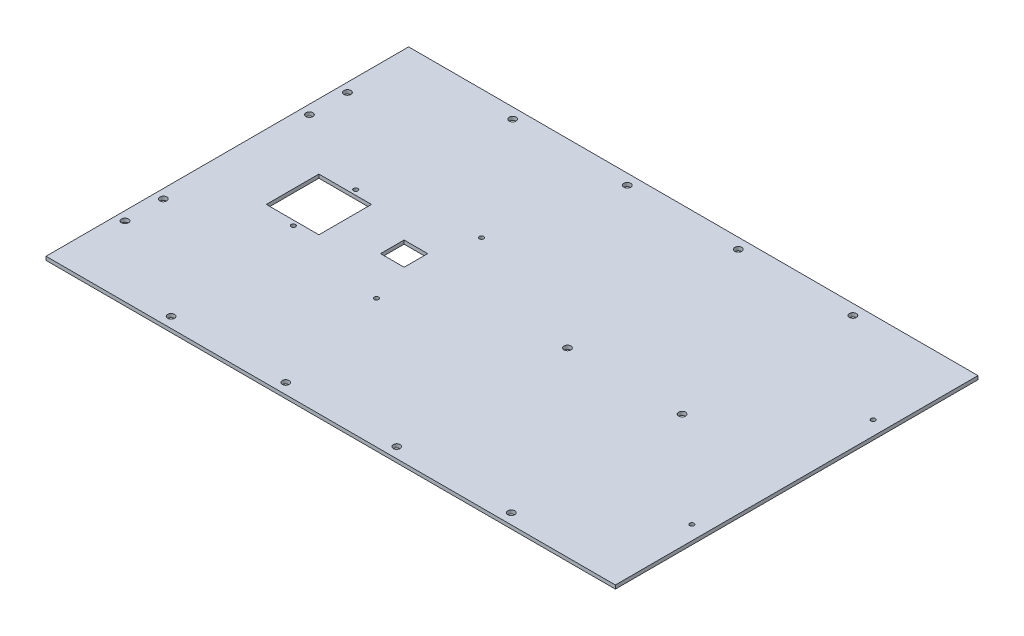
SolidWorks part; units mm, degrees
ref_plane "Front Plane" through (0, 0, 0) normal (0, 0, 1) x (1, 0, 0)
ref_plane "Top Plane" through (0, 0, 0) normal (0, 1, 0) x (1, 0, 0)
ref_plane "Right Plane" through (0, 0, 0) normal (1, 0, 0) x (0, 0, -1)
sketch "Sketch1" plane through (0, 0, 0) normal (0, 1, 0) x (1, 0, 0)
  line L0 (0, 63.5) -> (0, -63.5)
  line L1 (-199.39, 63.5) -> (199.39, 63.5)
  line L2 (-199.39, 63.5) -> (-199.39, -63.5)
  line L3 (-199.39, -63.5) -> (199.39, -63.5)
  line L4 (199.39, 63.5) -> (199.39, -63.5)
  dimension "D1" = 398.78
  dimension "D2" = 127
extrude "Boss-Extrude1" add sketch "Sketch1" along normal blind 2.54 contours L2 L3 L0 L1 | L4 L1 L0 L3
hole_wizard "#11 (0.191) Diameter Hole1" positions "Sketch6" profile "Sketch5" hole size "#11" standard "ANSI Inch" end condition through all
sketch "Sketch6" plane through (0, 2.54, 0) normal (0, 1, 0) x (1, 0, 0)
  line L0 (-199.39, 63.5) -> (-199.39, -63.5) construction
  line L1 (-199.39, -63.5) -> (199.39, -63.5) construction
  point P0 (-193.167, -14.4018)
  point P2 (-193.04, 12.3444)
  dimension "D1" = 6.223
  dimension "D2" = 49.0982
  dimension "D4" = 75.8444
sketch "Sketch5" plane through (-193.167, 2.54, 14.4018) normal (1, 0, 0) x (0, 0, 1)
  line L0 (0, 0) -> (0, 2.54)
  line L1 (0, 2.54) -> (2.4257, 2.54)
  line L2 (2.4257, 2.54) -> (2.4257, 0)
  line L5 (2.4257, 0) -> (0, 0)
  line L11 (0, -6.35) -> (0, 107.95) construction
  dimension "Thru Hole Dia." = 4.8514
  dimension "Thru Hole Depth" = 2.54
sketch "Sketch8" plane through (0, 2.54, 0) normal (0, 1, 0) x (1, 0, 0)
  line L0 (-199.39, 63.5) -> (199.39, 63.5) construction
  line L1 (-153.67, 63.5) -> (-116.84, 63.5)
  line L2 (-153.67, 63.5) -> (-153.67, 45.085)
  line L3 (-153.67, 45.085) -> (-116.84, 45.085)
  line L4 (-116.84, 63.5) -> (-116.84, 45.085)
  line L5 (-199.39, 63.5) -> (-199.39, -63.5) construction
  line L8 (-83.82, 63.5) -> (-67.31, 63.5)
  line L9 (-83.82, 63.5) -> (-83.82, 55.245)
  line L10 (-83.82, 55.245) -> (-67.31, 55.245)
  line L11 (-67.31, 63.5) -> (-67.31, 55.245)
  dimension "D1" = 18.415
  dimension "D2" = 36.83
  dimension "D3" = 45.72
  dimension "D4" = 16.51
  dimension "D5" = 8.255
  dimension "D6" = 33.02
hole_wizard "#11 (0.191) Diameter Hole2" positions "Sketch10" profile "Sketch9" hole size "#11" standard "ANSI Inch" end condition through all
sketch "Sketch10" plane through (0, 2.54, 0) normal (0, 1, 0) x (1, 0, 0)
  line L0 (-199.39, 63.5) -> (-199.39, -63.5) construction
  line L1 (199.39, 63.5) -> (199.39, -63.5) construction
  point P0 (-119.126, -56.1278)
  point P2 (-38.862, -56.1278)
  point P4 (38.862, -56.1278)
  point P6 (119.126, -56.1278)
  dimension "D1" = 80.264
  dimension "D2" = 80.264
  dimension "D3" = 80.264
  dimension "D4" = 80.264
sketch "Sketch9" plane through (-119.126, 2.54, 56.1278) normal (1, 0, 0) x (0, 0, 1)
  line L0 (0, 0) -> (0, 2.54)
  line L1 (0, 2.54) -> (2.4257, 2.54)
  line L2 (2.4257, 2.54) -> (2.4257, 0)
  line L5 (2.4257, 0) -> (0, 0)
  line L11 (0, -6.35) -> (0, 107.95) construction
  dimension "Thru Hole Dia." = 4.8514
  dimension "Thru Hole Depth" = 2.54
extrude "Cut-Extrude1" cut sketch "Sketch8" against normal blind 2.54
mirror "Mirror6" about plane through (0, 2.54, -63.5) normal (0, 0, -1) of "Cut-Extrude1", "#11 (0.191) Diameter Hole1", "#11 (0.191) Diameter Hole2", "Boss-Extrude1"
hole_wizard "#11 (0.191) Diameter Hole3" positions "Sketch14" profile "Sketch13" hole size "#11" standard "ANSI Inch" end condition through all
sketch "Sketch14" plane through (0, 2.54, 0) normal (0, 1, 0) x (1, 0, 0)
  point P0 (119.126, 63.5)
  point P2 (38.862, 63.5)
sketch "Sketch13" plane through (119.126, 2.54, -63.5) normal (1, 0, 0) x (0, 0, 1)
  line L0 (0, 0) -> (0, 2.54)
  line L1 (0, 2.54) -> (2.4257, 2.54)
  line L2 (2.4257, 2.54) -> (2.4257, 0)
  line L5 (2.4257, 0) -> (0, 0)
  line L11 (0, -6.35) -> (0, 107.95) construction
  dimension "Thru Hole Dia." = 4.8514
  dimension "Thru Hole Depth" = 2.54
hole_wizard "#31 (0.12) Diameter Hole2" positions "Sketch19" profile "Sketch18" hole size "#31" standard "ANSI Inch" end condition through all
sketch "Sketch19" plane through (0, 2.54, 0) normal (0, 1, 0) x (1, 0, 0)
  line L2 (-153.67, 81.915) -> (-116.84, 81.915) construction
  line L3 (-153.67, 45.085) -> (-116.84, 45.085) construction
  line L4 (-199.39, 190.5) -> (-199.39, -63.5) construction
  point P0 (-131.318, 41.656)
  point P2 (-131.318, 85.344)
  dimension "D1" = 43.688
  dimension "D2" = 3.429
  dimension "D3" = 3.429
  dimension "D4" = 68.072
sketch "Sketch18" plane through (-131.318, 2.54, -41.656) normal (1, 0, 0) x (0, 0, 1)
  line L0 (0, 0) -> (0, 2.54)
  line L1 (0, 2.54) -> (1.524, 2.54)
  line L2 (1.524, 2.54) -> (1.524, 0)
  line L5 (1.524, 0) -> (0, 0)
  line L11 (0, -6.35) -> (0, 107.95) construction
  dimension "Thru Hole Dia." = 3.048
  dimension "Thru Hole Depth" = 2.54
hole_wizard "#31 (0.12) Diameter Hole3" positions "Sketch21" profile "Sketch20" hole size "#31" standard "ANSI Inch" end condition through all
sketch "Sketch21" plane through (0, 2.54, 0) normal (0, 1, 0) x (1, 0, 0)
  line L0 (-199.39, 190.5) -> (-199.39, -63.5) construction
  line L2 (-83.82, 71.755) -> (-67.31, 71.755) construction
  point P0 (-58.166, 100.33)
  point P2 (-58.166, 26.67)
  dimension "D1" = 141.224
  dimension "D2" = 73.66
  dimension "D3" = 28.575
sketch "Sketch20" plane through (-58.166, 2.54, -100.33) normal (1, 0, 0) x (0, 0, 1)
  line L0 (0, 0) -> (0, 2.54)
  line L1 (0, 2.54) -> (1.524, 2.54)
  line L2 (1.524, 2.54) -> (1.524, 0)
  line L5 (1.524, 0) -> (0, 0)
  line L11 (0, -6.35) -> (0, 107.95) construction
  dimension "Thru Hole Dia." = 3.048
  dimension "Thru Hole Depth" = 2.54
hole_wizard "1/8 (0.125) Diameter Hole1" positions "Sketch23" profile "Sketch22" hole size "1/8" standard "ANSI Inch" end condition through all
sketch "Sketch23" plane through (0, 2.54, 0) normal (0, 1, 0) x (1, 0, 0)
  line L0 (-199.39, -63.5) -> (199.39, -63.5) construction
  line L1 (-199.39, 190.5) -> (199.39, 190.5) construction
  line L2 (199.39, 190.5) -> (199.39, -63.5) construction
  point P0 (189.484, 0)
  point P2 (189.484, 127)
  dimension "D1" = 63.5
  dimension "D2" = 63.5
  dimension "D3" = 9.906
sketch "Sketch22" plane through (189.484, 2.54, 0) normal (1, 0, 0) x (0, 0, 1)
  line L0 (0, 0) -> (0, 2.54)
  line L1 (0, 2.54) -> (1.524, 2.54)
  line L2 (1.524, 2.54) -> (1.524, 0)
  line L5 (1.524, 0) -> (0, 0)
  line L11 (0, -6.35) -> (0, 107.95) construction
  dimension "Thru Hole Dia." = 3.048
  dimension "Thru Hole Depth" = 2.54
